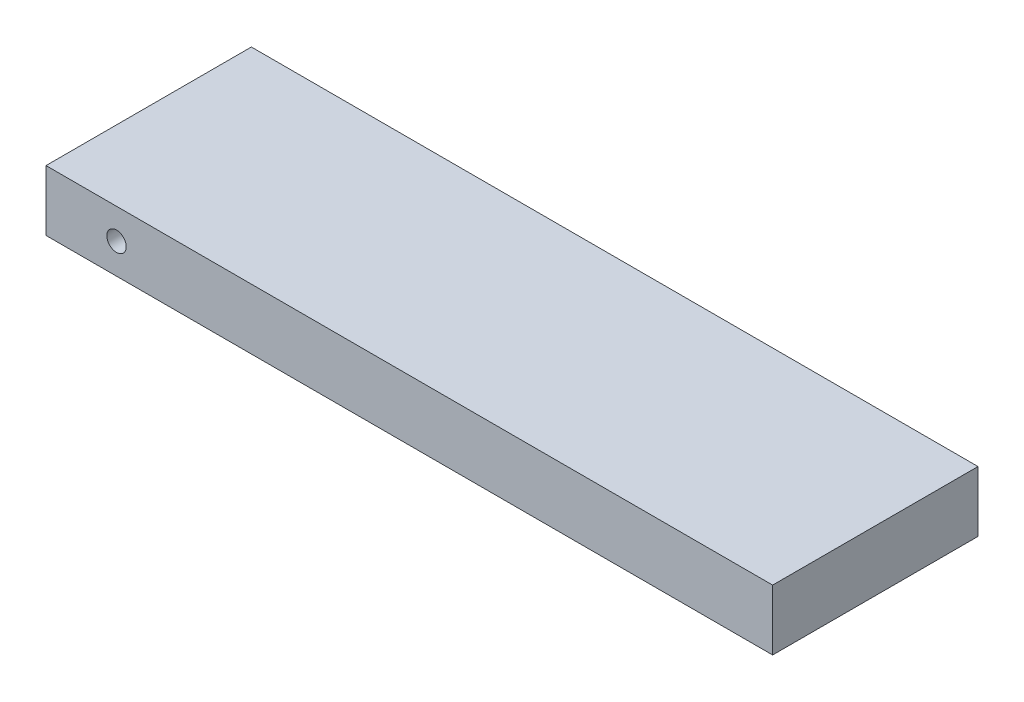
SolidWorks part; units mm, degrees
ref_plane "Front Plane" through (0, 0, 0) normal (0, 0, 1) x (1, 0, 0)
ref_plane "Top Plane" through (0, 0, 0) normal (0, 1, 0) x (1, 0, 0)
ref_plane "Right Plane" through (0, 0, 0) normal (1, 0, 0) x (0, 0, -1)
sketch "Sketch1" plane through (0, 0, 0) normal (0, 1, 0) x (1, 0, 0)
  line L0 (-33.3492, -316.4272) -> (98.3304, -316.4272) construction
  line L1 (-50.2303, -307.9485) -> (9.7697, -307.9485)
  line L2 (-50.2303, -307.9485) -> (-50.2303, -324.9058)
  line L3 (-50.2303, -324.9058) -> (9.7697, -324.9058)
  line L4 (9.7697, -307.9485) -> (9.7697, -324.9058)
  point P4 (-50.2303, -316.4272)
  point P7 (9.7697, -316.4272)
  point P8 (0, 0)
  dimension "D1" = 16.9573
  dimension "D2" = 60
extrude "Boss-Extrude1" add sketch "Sketch1" along normal blind 5 contours L1 L4 L3 L2
sketch "Sketch2" plane through (0, 0, 324.9058) normal (0, 0, 1) x (1, 0, 0)
  line L0 (-44.4068, 5) -> (-44.4068, 0) construction
  line L1 (-50.2303, 5) -> (9.7697, 5) construction
  line L2 (-50.2303, 0) -> (9.7697, 0) construction
  point P8 (-44.4068, 2.5)
hole_wizard "Tap Drill for M2x0.4 Tap1" positions "Sketch3" profile "Sketch4" hole size "M2x0.4" standard "ANSI Metric" end condition through all
sketch "Sketch3" plane through (0, 0, 324.9058) normal (0, 0, 1) x (1, 0, 0)
  point P0 (-44.4068, 2.5)
sketch "Sketch4" plane through (-44.4068, 2.5, 324.9058) normal (1, 0, 0) x (0, -1, 0)
  line L0 (0, 0) -> (0, 16.9573)
  line L1 (0, 16.9573) -> (0.8, 16.9573)
  line L2 (0.8, 16.9573) -> (0.8, 0)
  line L5 (0.8, 0) -> (0, 0)
  line L11 (0, -6.35) -> (0, 107.95) construction
  dimension "Thru Hole Dia." = 1.6
  dimension "Thru Hole Depth" = 16.9573
